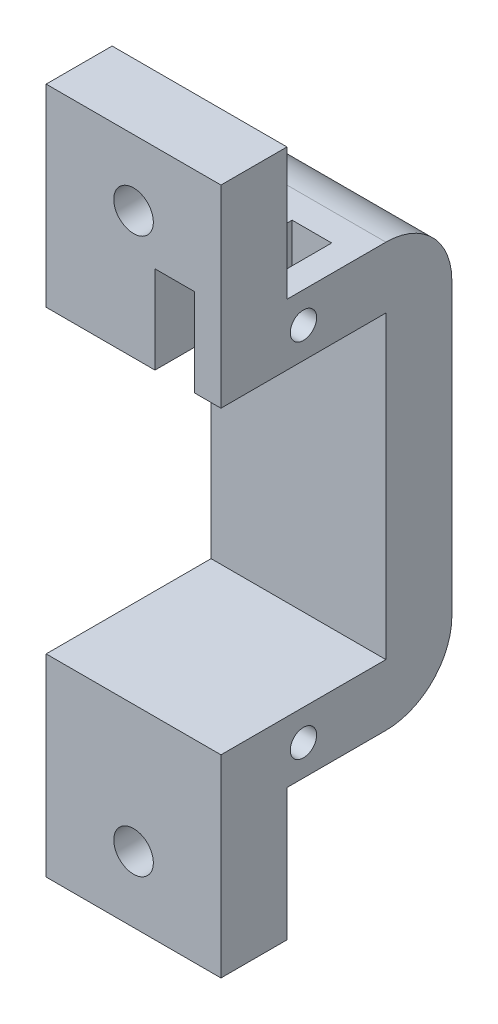
SolidWorks part; units mm, degrees
material "ABS"
ref_plane "Plano frontal" through (0, 0, 0) normal (0, 0, 1) x (1, 0, 0)
ref_plane "Plano superior" through (0, 0, 0) normal (0, 1, 0) x (1, 0, 0)
ref_plane "Plano direito" through (0, 0, 0) normal (1, 0, 0) x (0, 0, -1)
sketch "Esboço1" plane through (0, 0, 0) normal (0, 1, 0) x (1, 0, 0)
  line L1 (-21.7379, -6.1618) -> (-8.4879, -6.1618)
  line L2 (-21.7379, -6.1618) -> (-21.7379, -18.6618)
  line L3 (-21.7379, -18.6618) -> (-8.4879, -18.6618)
  line L4 (-8.4879, -6.1618) -> (-8.4879, -18.6618)
extrude "Ressalto-extrusão1" add sketch "Esboço1" against normal blind 4.65
sketch "Esboço2" plane through (0, 0, 6.1618) normal (0, 0, -1) x (-1, 0, 0)
  line L1 (21.7379, 0) -> (8.4879, 0)
  line L2 (21.7379, 0) -> (21.7379, -32.05)
  line L3 (21.7379, -32.05) -> (8.4879, -32.05)
  line L4 (8.4879, 0) -> (8.4879, -32.05)
extrude "Ressalto-extrusão2" add sketch "Esboço2" along normal blind 5
sketch "Esboço3" plane through (0, 0, 6.1618) normal (0, 0, 1) x (1, 0, 0)
  line L0 (-21.7379, -32.05) -> (-21.7379, -4.65) construction
  line L1 (-8.4879, -32.05) -> (-21.7379, -32.05)
  line L2 (-8.4879, -32.05) -> (-8.4879, -27.4)
  line L3 (-8.4879, -27.4) -> (-21.7379, -27.4)
  line L4 (-21.7379, -32.05) -> (-21.7379, -27.4)
extrude "Ressalto-extrusão3" add sketch "Esboço3" along normal blind 12.5
sketch "Esboço4" plane through (0, -32.05, 0) normal (0, -1, 0) x (-1, 0, 0)
  line L0 (8.4879, -1.1618) -> (8.4879, -18.6618) construction
  line L1 (21.7379, -18.6618) -> (8.4879, -18.6618)
  line L2 (21.7379, -18.6618) -> (21.7379, -13.6618)
  line L3 (21.7379, -13.6618) -> (8.4879, -13.6618)
  line L4 (8.4879, -18.6618) -> (8.4879, -13.6618)
extrude "Ressalto-extrusão4" add sketch "Esboço4" along normal blind 10
sketch "Esboço5" plane through (0, 0, 0) normal (0, 1, 0) x (1, 0, 0)
  line L0 (-8.4879, -18.6618) -> (-8.4879, -1.1618) construction
  line L1 (-21.7379, -18.6618) -> (-8.4879, -18.6618)
  line L2 (-21.7379, -18.6618) -> (-21.7379, -13.6618)
  line L3 (-21.7379, -13.6618) -> (-8.4879, -13.6618)
  line L4 (-8.4879, -18.6618) -> (-8.4879, -13.6618)
extrude "Ressalto-extrusão5" add sketch "Esboço5" along normal blind 10
sketch "Esboço6" plane through (0, 0, 13.6618) normal (0, 0, -1) x (-1, 0, 0)
  line L0 (8.4879, 10) -> (21.7379, 10) construction
  line L1 (21.7379, 10) -> (21.7379, 0) construction
  line L2 (21.7379, -42.05) -> (8.4879, -42.05) construction
  line L3 (21.7379, -42.05) -> (21.7379, -32.05) construction
  circle A0 centre (15.1129, 5) radius 1.5
  circle A1 centre (15.1129, -37.05) radius 1.5
  point P10 (15.1129, -42.05)
  point P13 (21.7379, -37.05)
  dimension "D1" = 5
  dimension "D2" = 6.625
  dimension "D3" = 5
  dimension "D4" = 6.625
extrude "Corte-extrusão1" cut sketch "Esboço6" against normal blind 10
sketch "Esboço7" plane through (-8.4879, 0, 0) normal (1, 0, 0) x (0, 0, -1)
  line L0 (-18.6618, -4.65) -> (-18.6618, 10) construction
  line L1 (-13.6618, 0) -> (-1.1618, 0) construction
  circle A0 centre (-12.4118, -2.325) radius 1
  dimension "D1" = 6.25
  dimension "D2" = 2.325
sketch "Esboço8" plane through (-8.4879, 0, 0) normal (1, 0, 0) x (0, 0, -1)
  line L0 (-18.6618, -42.05) -> (-18.6618, -27.4) construction
  line L1 (-1.1618, -32.05) -> (-13.6618, -32.05) construction
  circle A0 centre (-12.4118, -29.725) radius 1
  dimension "D1" = 6.25
  dimension "D2" = 2.325
extrude "Corte-extrusão2" cut sketch "Esboço7" against normal through all
extrude "Corte-extrusão3" cut sketch "Esboço8" against normal through all
sketch "Esboço9" plane through (0, 0, 0) normal (0, 1, 0) x (1, 0, 0)
  line L0 (-8.4879, -13.6618) -> (-8.4879, -1.1618) construction
  line L1 (-13.4879, -18.6618) -> (-10.4879, -18.6618)
  line L2 (-13.4879, -18.6618) -> (-13.4879, -8.2708)
  line L3 (-13.4879, -8.2708) -> (-10.4879, -8.2708)
  line L4 (-10.4879, -18.6618) -> (-10.4879, -8.2708)
  line L7 (-21.7379, -18.6618) -> (-8.4879, -18.6618) construction
  dimension "D1" = 2
  dimension "D2" = 3
  dimension "D3" = 0
extrude "Corte-extrusão4" cut sketch "Esboço9" against normal blind 10
sketch "Esboço10" plane through (0, 0, 13.6618) normal (0, 0, -1) x (-1, 0, 0)
  line L0 (8.4879, 0) -> (10.4879, 0) construction
  line L1 (10.4879, 0) -> (13.4879, 0)
  line L2 (10.4879, 0) -> (10.4879, 2)
  line L3 (10.4879, 2) -> (13.4879, 2)
  line L4 (13.4879, 0) -> (13.4879, 2)
  line L5 (8.4879, 10) -> (8.4879, 0) construction
  dimension "D1" = 2
extrude "Corte-extrusão5" cut sketch "Esboço10" against normal blind 10
fillet "Filete1" radius 5 1 edges at (-15.1129, 0, 1.1618)
fillet "Filete2" radius 5 1 edges at (-15.1129, -32.05, 1.1618)
